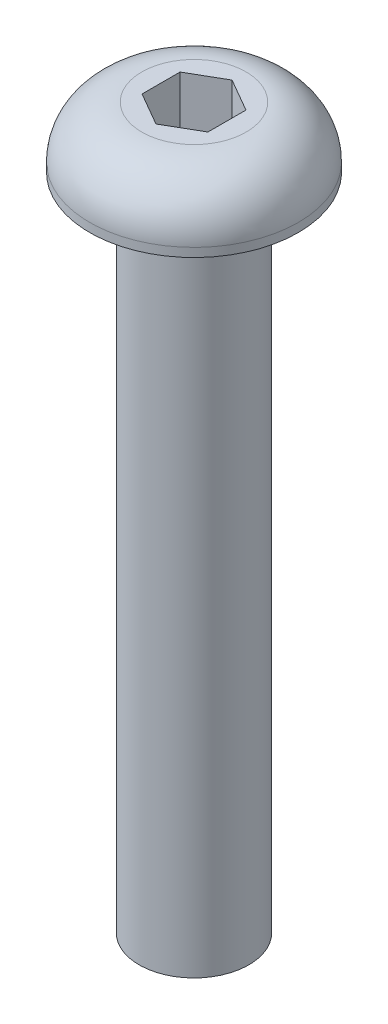
SolidWorks part; units mm, degrees
ref_plane "Plano frontal" through (0, 0, 0) normal (0, 0, 1) x (1, 0, 0)
ref_plane "Plano superior" through (0, 0, 0) normal (0, 1, 0) x (1, 0, 0)
ref_plane "Plano direito" through (0, 0, 0) normal (1, 0, 0) x (0, 0, -1)
sketch "Esboço1" plane through (0, 0, 0) normal (0, 0, 1) x (1, 0, 0)
  line L0 (0, 0) -> (2.5, 0)
  line L1 (2.5, 0) -> (2.5, 30)
  line L2 (2.5, 30) -> (4.75, 30)
  line L3 (4.75, 30) -> (4.75, 30.4)
  line L4 (2.375, 32.775) -> (0, 32.775)
  line L5 (0, 32.775) -> (0, 0) construction
  line L6 (0, 0) -> (0, 32.775)
  arc A0 (2.375, 32.775) -> (4.75, 30.4) centre (2.375, 30.4) cw
  dimension "D1" = 5
  dimension "D2" = 9.5
  dimension "D3" = 4.75
  dimension "D4" = 0.4
  dimension "D5" = 30
revolve "Revolução1" add sketch "Esboço1" angle 360 about L5
sketch "Esboço2" plane through (0, 32.775, 0) normal (0, 1, 0) x (1, 0, 0)
  line L1 (-1.5, 0.866) -> (-1.5, -0.866)
  line L2 (-1.5, -0.866) -> (0, -1.7321)
  line L3 (0, -1.7321) -> (1.5, -0.866)
  line L4 (1.5, -0.866) -> (1.5, 0.866)
  line L5 (1.5, 0.866) -> (0, 1.7321)
  line L6 (0, 1.7321) -> (-1.5, 0.866)
  circle A0 centre (0, 0) radius 1.5 construction
  dimension "D1" = 3
extrude "Corte-extrusão1" cut sketch "Esboço2" against normal blind 4
